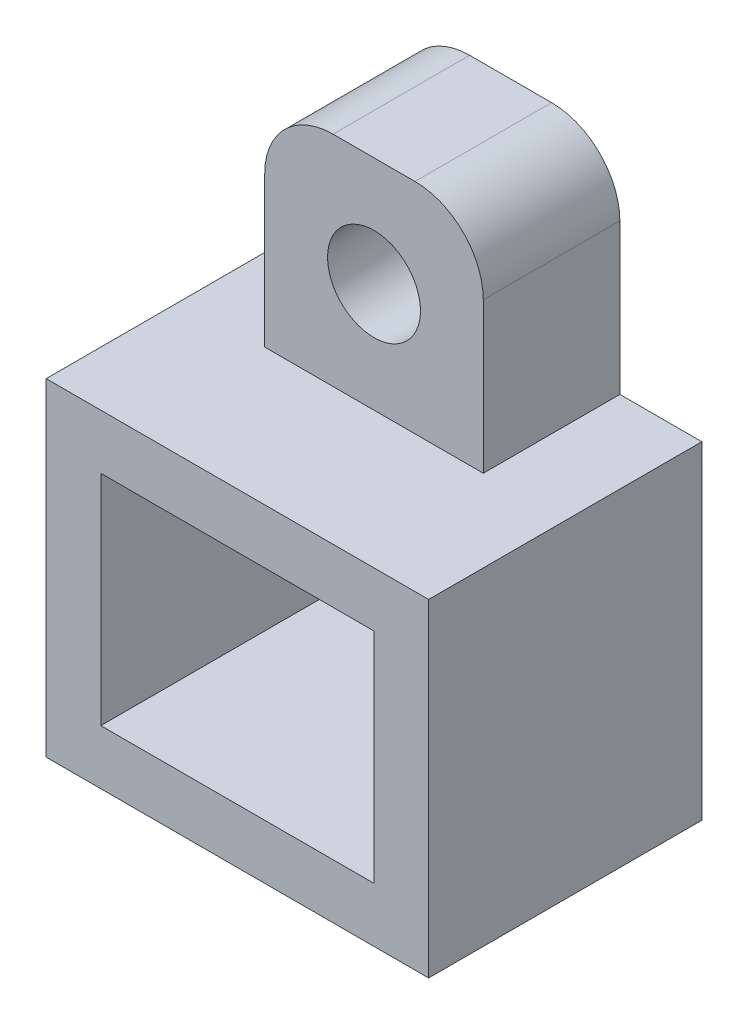
SolidWorks part; units mm, degrees
material "ABS"
ref_plane "Front Plane" through (0, 0, 0) normal (0, 0, 1) x (1, 0, 0)
ref_plane "Top Plane" through (0, 0, 0) normal (0, 1, 0) x (1, 0, 0)
ref_plane "Right Plane" through (0, 0, 0) normal (1, 0, 0) x (0, 0, -1)
sketch "Sketch1" plane through (0, 0, 0) normal (0, 0, 1) x (1, 0, 0)
  line L1 (-5, 4) -> (5, 4)
  line L2 (-5, 4) -> (-5, -4)
  line L3 (-5, -4) -> (5, -4)
  line L4 (5, 4) -> (5, -4)
  line L5 (-5, 4) -> (5, -4) construction
  line L6 (-5, -4) -> (5, 4) construction
  point P0 (0, 0)
  dimension "D1" = 8
  dimension "D2" = 10
sketch "Sketch2" plane through (0, 0, 0) normal (0, 0, 1) x (1, 0, 0)
  line L0 (5, 4) -> (5, -4) construction
  line L1 (-7, 6) -> (7, 6)
  line L2 (-7, 6) -> (-7, -6)
  line L3 (-7, -6) -> (7, -6)
  line L4 (7, 6) -> (7, -6)
  line L5 (-7, 6) -> (7, -6) construction
  line L6 (-7, -6) -> (7, 6) construction
  line L7 (-5, 4) -> (5, 4) construction
  point P0 (0, 0)
  dimension "D1" = 2
  dimension "D2" = 2
sketch "Sketch3" plane through (0, 0, 0) normal (0, 0, 1) x (1, 0, 0)
  line L0 (-7, 6) -> (7, 6) construction
  line L1 (-4, 6) -> (4, 6)
  line L2 (-4, 6) -> (-4, 14)
  line L3 (-4, 14) -> (4, 14)
  line L4 (4, 6) -> (4, 14)
  point P6 (0, 6)
  dimension "D1" = 8
  dimension "D2" = 8
extrude "Boss-Extrude1" add sketch "Sketch2" along normal blind 10
extrude "Cut-Extrude2" cut sketch "Sketch1" along normal through all
sketch "Sketch4" plane through (0, 0, 0) normal (0, 0, 1) x (1, 0, 0)
  line L0 (4, 6) -> (4, 14) construction
  line L1 (-4, 14) -> (4, 14) construction
  circle A0 centre (0, 10) radius 1.7
  point P4 (4, 10)
  point P7 (0, 14)
  dimension "D1" = 3.4
extrude "Boss-Extrude2" add sketch "Sketch3" along normal blind 5
extrude "Cut-Extrude3" cut sketch "Sketch4" along normal through all
fillet "Fillet1" radius 2.5 2 edges at (4, 14, 2.5) (-4, 14, 2.5)
